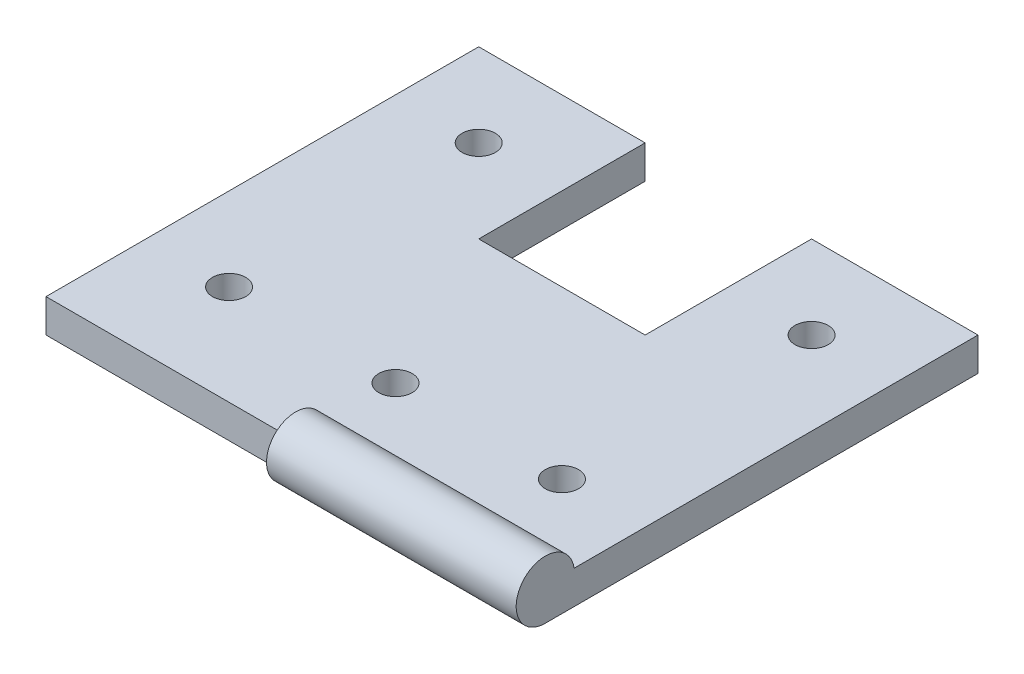
SolidWorks part; units mm, degrees
ref_plane "Front Plane" through (0, 0, 0) normal (0, 0, 1) x (1, 0, 0)
ref_plane "Top Plane" through (0, 0, 0) normal (0, 1, 0) x (1, 0, 0)
ref_plane "Right Plane" through (0, 0, 0) normal (1, 0, 0) x (0, 0, -1)
sketch "Sketch1" plane through (0, 0, 0) normal (0, 1, 0) x (1, 0, 0)
  line L2 (18.0696, -160.0434) -> (3.0696, -160.0434)
  line L3 (18.0696, -160.0434) -> (18.0696, -173.0434)
  line L4 (18.0696, -173.0434) -> (3.0696, -173.0434)
  line L5 (3.0696, -160.0434) -> (3.0696, -173.0434)
  dimension "D1" = 13
  dimension "D2" = 15
extrude "Boss-Extrude1" add sketch "Sketch1" along normal blind 1
sketch "Sketch2" plane through (18.0696, 0, 0) normal (1, 0, 0) x (0, 0, -1)
  circle A0 centre (-173.0434, 0.875) radius 0.875
  point P4 (0, 0)
  dimension "D1" = 1.75
extrude "Boss-Extrude2" add sketch "Sketch2" against normal blind 7.5
sketch "Sketch3" plane through (0, 0, 0) normal (0, -1, 0) x (-1, 0, 0)
  line L0 (-18.0696, -160.0434) -> (-3.0696, -160.0434) construction
  line L1 (-8.0696, -160.0434) -> (-13.0696, -160.0434)
  line L2 (-8.0696, -160.0434) -> (-8.0696, -165.0434)
  line L3 (-8.0696, -165.0434) -> (-13.0696, -165.0434)
  line L4 (-13.0696, -160.0434) -> (-13.0696, -165.0434)
  point P4 (-10.5696, -160.0434)
  point P7 (-10.5696, -160.0434)
  dimension "D1" = 5
  dimension "D2" = 5
extrude "Cut-Extrude1" cut sketch "Sketch3" against normal blind 10
sketch "Sketch4" plane through (0, 1, 0) normal (0, 1, 0) x (1, 0, 0)
  line L0 (15.5696, -170.0434) -> (5.5696, -170.0434) construction
  line L1 (5.5696, -170.0434) -> (5.5696, -162.5434) construction
  line L2 (5.5696, -162.5434) -> (15.5696, -162.5434) construction
  line L3 (15.5696, -162.5434) -> (15.5696, -170.0434) construction
  line L4 (18.0696, -172.1774) -> (18.0696, -160.0434) construction
  line L5 (3.0696, -160.0434) -> (3.0696, -173.0434) construction
  line L6 (8.0696, -160.0434) -> (3.0696, -160.0434) construction
  circle A0 centre (15.5696, -162.5434) radius 0.5
  circle A1 centre (15.5696, -170.0434) radius 0.5
  circle A2 centre (10.5696, -170.0434) radius 0.5
  circle A3 centre (5.5696, -170.0434) radius 0.5
  circle A4 centre (5.5696, -162.5434) radius 0.5
  point P10 (0, 0)
  point P11 (10.5696, -170.0434)
  dimension "D1" = 1
  dimension "D2" = 2.5
  dimension "D3" = 2.5
  dimension "D4" = 2.5
  dimension "D5" = 10
extrude "Cut-Extrude2" cut sketch "Sketch4" against normal through all
